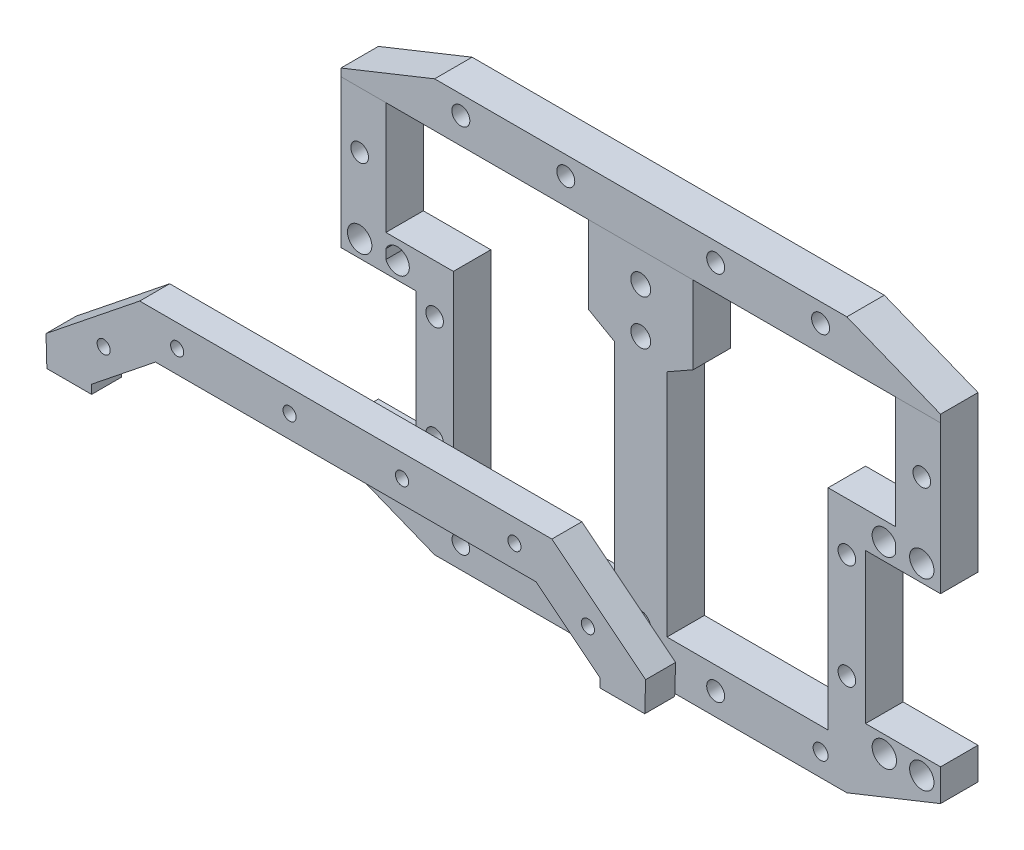
SolidWorks part; units mm, degrees
ref_plane "Ebene vorne" through (0, 0, 0) normal (0, 0, 1) x (1, 0, 0)
ref_plane "Ebene oben" through (0, 0, 0) normal (0, 1, 0) x (1, 0, 0)
ref_plane "Ebene rechts" through (0, 0, 0) normal (1, 0, 0) x (0, 0, -1)
sketch "Sketch1" plane through (0, 0, 0) normal (0, 0, 1) x (1, 0, 0)
  line L0 (68, 6.75) -> (68, 9.25)
  line L1 (-68, 6.75) -> (-68, 9.25)
  line L2 (-50, 13) -> (-68, 13)
  line L3 (80, -36.5) -> (60, -36.5)
  line L4 (60, -36.5) -> (60, 3.5)
  line L5 (60, 3.5) -> (80, 3.5)
  line L6 (80, 3.5) -> (80, 45)
  line L7 (80, 45) -> (55, 55)
  line L8 (55, 55) -> (-55, 55)
  line L9 (-55, 55) -> (-80, 45)
  line L10 (-80, 45) -> (-80, 3.5)
  line L11 (-80, 3.5) -> (-60, 3.5)
  line L12 (-60, 3.5) -> (-60, -36.5)
  line L13 (-60, -36.5) -> (-80, -36.5)
  line L14 (-80, -36.5) -> (-80, -45)
  line L15 (-80, -45) -> (-55, -55)
  line L16 (-55, -55) -> (55, -55)
  line L17 (55, -55) -> (80, -45)
  line L18 (80, -45) -> (80, -36.5)
  line L19 (-50, -43) -> (-50, 13)
  line L20 (-7, -43) -> (-50, -43)
  line L21 (50, -43) -> (7, -43)
  line L22 (50, 13) -> (50, -43)
  line L23 (50, 13) -> (68, 13)
  line L24 (68, 13) -> (68, 43)
  line L25 (68, 43) -> (14, 43)
  line L26 (14, 43) -> (14, 22.265)
  line L27 (14, 22.265) -> (7, 18.2936)
  line L28 (-7, -43) -> (-7, 18.2936)
  line L29 (-14, 22.265) -> (-7, 18.2936)
  line L30 (-14, 43) -> (-14, 22.265)
  line L31 (-68, 43) -> (-14, 43)
  line L32 (-68, 13) -> (-68, 43)
  line L33 (7, -43) -> (7, 18.2936)
  circle A0 centre (-48, 50) radius 2.3996
  circle A1 centre (-20, 50) radius 2.3996
  circle A2 centre (0, 35) radius 2.65
  circle A3 centre (0, 23) radius 2.65
  circle A4 centre (20, 50) radius 2.3996
  circle A5 centre (48, 50) radius 2.3996
  circle A6 centre (75, 28) radius 2.351
  circle A7 centre (75, 8) radius 3.25
  circle A8 centre (55, 0) radius 2.35
  arc A9 (68, 9.25) -> (68, 6.75) centre (65, 8) ccw
  circle A10 centre (55, -28) radius 2.35
  circle A11 centre (75, -41) radius 3.25
  circle A12 centre (65, -41) radius 3.25
  circle A13 centre (48, -49) radius 2
  circle A14 centre (20, -49) radius 2.3996
  circle A15 centre (0, -43) radius 2.65
  circle A16 centre (-20, -49) radius 2.4776
  circle A17 centre (-48, -49) radius 2.3542
  circle A18 centre (-75, -41) radius 3.25
  circle A19 centre (-65, -41) radius 3.25
  circle A20 centre (-55, -28) radius 2.35
  circle A21 centre (-55, 0) radius 2.35
  arc A22 (-68, 6.75) -> (-68, 9.25) centre (-65, 8) ccw
  circle A23 centre (-75, 8) radius 3.25
  circle A24 centre (-75, 28) radius 2.351
  dimension "D19" = 4.7992
  dimension "D1" = 110
  dimension "D2" = 25
  dimension "D3" = 10
  dimension "D4" = 8.5
  dimension "D5" = 20
  dimension "D6" = 40
  dimension "D7" = 20
  dimension "D8" = 41.5
  dimension "D9" = 30
  dimension "D10" = 56
  dimension "D11" = 43
  dimension "D12" = 18
  dimension "D13" = 61.2936
  dimension "D14" = 8.0481
  dimension "D15" = 119.568
  dimension "D16" = 20.735
  dimension "D17" = 54
  dimension "D18" = 5
  dimension "D21" = 5
  dimension "D22" = 25
  dimension "D23" = 111.801
  dimension "D24" = 158.199
  dimension "D25" = 20.735
  dimension "D26" = 7
  dimension "D27" = 61.2936
  dimension "D28" = 43
  dimension "D29" = 56
  dimension "D30" = 18
  dimension "D31" = 30
  dimension "D32" = 54
  dimension "D33" = 119.568
  dimension "D34" = 25
  dimension "D35" = 158.199
  dimension "D36" = 8.5
  dimension "D37" = 20
  dimension "D38" = 40
  dimension "D39" = 41.5
  dimension "D40" = 5
  dimension "D41" = 5
extrude "Boss-Extrude1" add sketch "Sketch1" along normal blind 10
ref_plane "Plane1" through (0, 0, 88.7) normal (0, 0, 1) x (1, 0, 0)
sketch "Sketch2" plane through (0, 0, 88.7) normal (0, 0, 1) x (1, 0, 0)
  line L0 (0, -55.004) -> (0, 42.996) construction
  line L3 (-80, 22.996) -> (80, 22.996) construction
  line L4 (-80, 22.996) -> (-55, 42.996)
  line L6 (-70, -55.004) -> (-77.9327, -48.3477)
  line L7 (-80, 22.996) -> (-77.9327, -48.3477)
  line L10 (-78.5511, -27.004) -> (78.5511, -27.004) construction
  line L11 (-67.8317, 17.3631) -> (-50.7906, 30.996)
  line L12 (-50.7906, 30.996) -> (50.7906, 30.996)
  line L15 (-65.6324, -43.004) -> (65.6324, -43.004)
  line L16 (-65.6324, -43.004) -> (-66.0937, -42.6169)
  line L17 (-66.3561, -33.5593) -> (-66.0937, -42.6169)
  line L20 (-75.2417, 36.996) -> (75.2417, 36.996) construction
  line L21 (-67, -11.34) -> (-67, 14.66)
  line L22 (-88.0533, 8.8697) -> (-38.2663, 48.6993) construction
  line L25 (-67, -11.34) -> (-66.7419, -20.2486)
  line L26 (-67, 14.66) -> (-67.8317, 17.3631)
  line L28 (-88.0533, -49.004) -> (88.0533, -49.004) construction
  line L29 (-70, -55.004) -> (70, -55.004)
  line L30 (-55, 42.996) -> (55, 42.996)
  line L31 (88.0533, 8.8697) -> (38.2663, 48.6993) construction
  line L32 (67, -11.34) -> (0, -11.34) construction
  line L33 (67, 14.66) -> (67.8317, 17.3631)
  line L34 (67, -11.34) -> (66.7419, -20.2486)
  line L35 (67, -11.34) -> (67, 14.66)
  line L36 (66.3561, -33.5593) -> (66.0937, -42.6169)
  line L37 (65.6324, -43.004) -> (66.0937, -42.6169)
  line L38 (67.8317, 17.3631) -> (50.7906, 30.996)
  line L39 (80, 22.996) -> (77.9327, -48.3477)
  line L40 (70, -55.004) -> (77.9327, -48.3477)
  line L41 (80, 22.996) -> (55, 42.996)
  circle A0 centre (-70, -27.004) radius 6
  arc A2 (-66.3561, -33.5593) -> (-66.7419, -20.2486) centre (-70, -27.004) ccw
  circle A4 centre (-45, 36.996) radius 1.75
  circle A5 centre (-15, 36.996) radius 1.75
  circle A8 centre (-64.6083, 27.6256) radius 1.75
  circle A10 centre (-15, -49.004) radius 1.75
  circle A11 centre (15, -49.004) radius 1.75
  circle A12 centre (64.6083, 27.6256) radius 1.75
  circle A13 centre (15, 36.996) radius 1.75
  circle A14 centre (45, 36.996) radius 1.75
  arc A15 (66.3561, -33.5593) -> (66.7419, -20.2486) centre (70, -27.004) cw
  circle A16 centre (70, -27.004) radius 6
  point P5 (0, 42.996)
  point P8 (0, -55.004)
  point P9 (0, -49.004)
  point P12 (0, 22.996)
  point P17 (0, -27.004)
  point P22 (0, 36.996)
  point P29 (0, -27.004)
  point P31 (0, 22.996)
  point P35 (0, -11.34)
  point P51 (-52.8953, 36.996)
  point P68 (0, -43.004)
  point P69 (0, 30.996)
  point P70 (52.8953, 36.996)
  dimension "D1" = 11.34
  dimension "D3" = 6
  dimension "D5" = 26
extrude "Boss-Extrude2" add sketch "Sketch2" against normal blind 8 separate body
sketch "Sketch3" plane through (0, 0, 88.7) normal (0, 0, 1) x (1, 0, 0)
  line L0 (0, -66.9319) -> (0, 70.2612) construction
  line L2 (121.6566, -66.3348) -> (-121.6566, -66.3348)
  line L3 (121.6566, -66.3348) -> (121.6566, 14.996)
  line L4 (121.6566, 14.996) -> (-121.6566, 14.996)
  line L5 (-121.6566, -66.3348) -> (-121.6566, 14.996)
  line L6 (121.6566, -66.3348) -> (-121.6566, 14.996) construction
  line L7 (121.6566, 14.996) -> (-121.6566, -66.3348) construction
  point P3 (0, -25.6694)
  dimension "D1" = 8
extrude "Cut-Extrude1" cut sketch "Sketch3" against normal blind 8
sketch "Sketch4" plane through (0, 0, 88.7) normal (0, 0, 1) x (1, 0, 0)
  line L0 (-67.8317, 17.3631) -> (-67.8317, 14.996)
  line L1 (-67.1034, 14.996) -> (-79.7682, 14.996) construction
  line L2 (-67.8317, 14.996) -> (-67.1034, 14.996)
  line L3 (-67.1034, 14.996) -> (-67.8317, 17.3631)
  line L4 (67.8317, 17.3631) -> (67.8317, 14.996)
  line L5 (79.7682, 14.996) -> (67.1034, 14.996) construction
  line L6 (67.8317, 14.996) -> (67.1034, 14.996)
  line L7 (67.1034, 14.996) -> (67.8317, 17.3631)
extrude "Cut-Extrude2" cut sketch "Sketch4" against normal blind 8
sketch3d "3DSketch2"
  line L0 (-80, 45, 10) -> (-80, 22.996, 80.7)
  line L1 (-55, 55, 10) -> (-55, 42.996, 80.7)
  line L2 (55, 55, 10) -> (55, 42.996, 80.7)
  line L3 (80, 45, 10) -> (80, 22.996, 80.7)
  line L4 (-14, 43, 10) -> (-50.7906, 30.996, 80.7)
  line L5 (14, 43, 10) -> (50.7906, 30.996, 80.7)
sketch "Sketch5" plane through (0, 0, 10) normal (0, 0, 1) x (1, 0, 0)
  line L0 (-98.0744, 42.996) -> (98.0744, 42.996)
  point P3 (0, 42.996)
split line "Split Line1"
sketch "Sketch6" plane through (0, 0, 10) normal (0, 0, 1) x (1, 0, 0)
  line L0 (-70, 49) -> (70, 49) construction
  line L1 (55, 55) -> (-55, 55) construction
  line L2 (80, 45) -> (55, 55) construction
  line L3 (-55, 55) -> (-80, 45) construction
  line L4 (68, 43) -> (14, 43) construction
  line L5 (-45, 55) -> (45, 55)
  line L6 (-45, 55) -> (-45, 43)
  line L7 (-45, 43) -> (45, 43)
  line L8 (45, 55) -> (45, 43)
  line L9 (-45, 55) -> (45, 43) construction
  line L10 (-45, 43) -> (45, 55) construction
  point P10 (0, 49)
  dimension "D1" = 6
  dimension "D2" = 90
